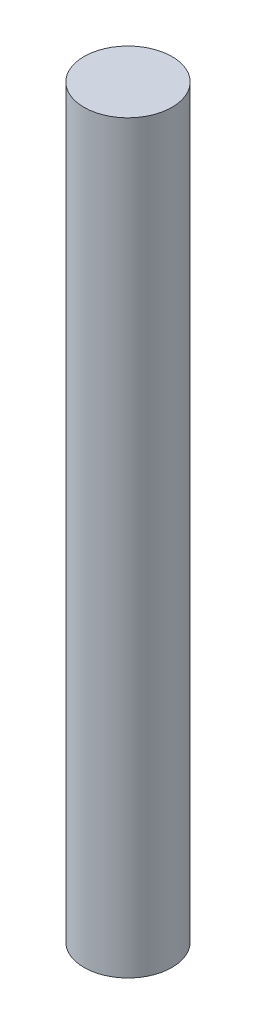
SolidWorks part; units mm, degrees
ref_plane "Front Plane" through (0, 0, 0) normal (0, 0, 1) x (1, 0, 0)
ref_plane "Top Plane" through (0, 0, 0) normal (0, 1, 0) x (1, 0, 0)
ref_plane "Right Plane" through (0, 0, 0) normal (1, 0, 0) x (0, 0, -1)
sketch "Sketch1" plane through (0, 0, 0) normal (0, 1, 0) x (1, 0, 0)
  circle A0 centre (0, 0) radius 3
  dimension "D1" = 6
extrude "Boss-Extrude1" add sketch "Sketch1" along normal mid plane 50.8
